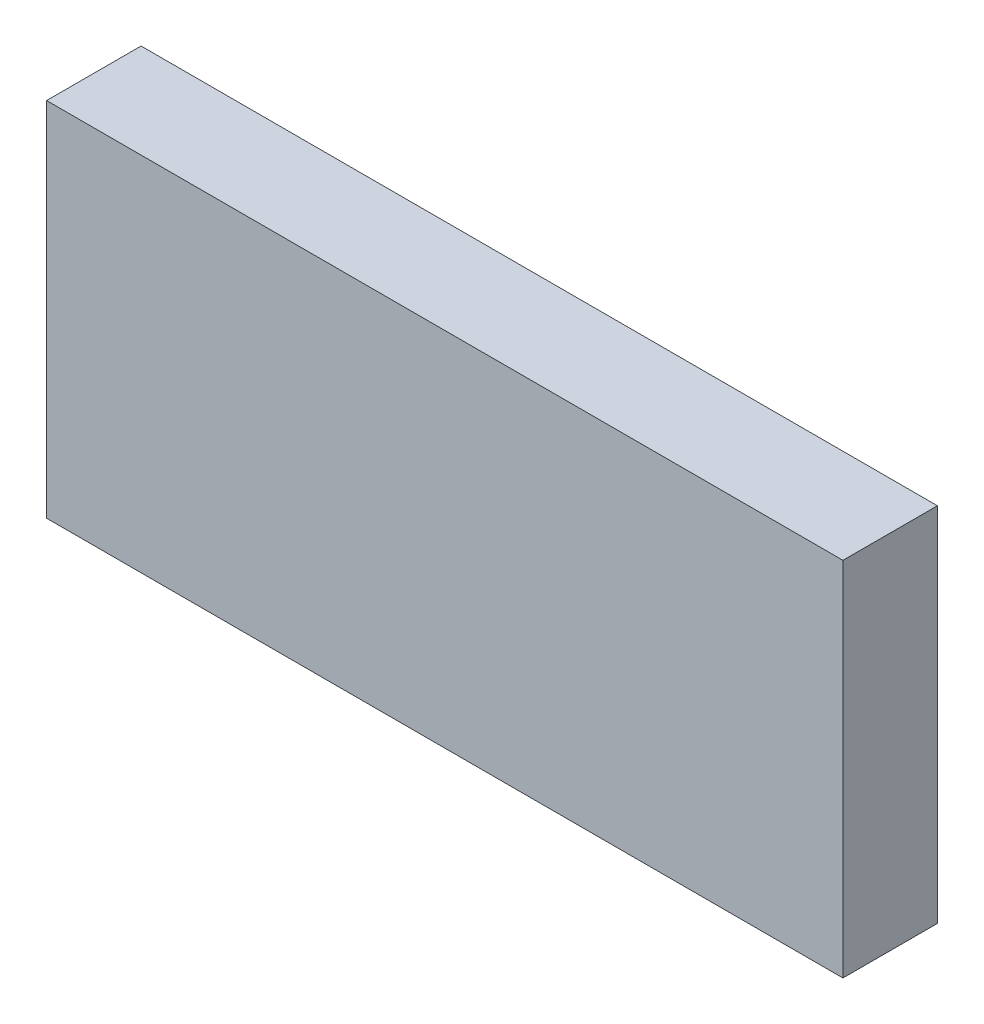
SolidWorks part; units mm, degrees
ref_plane "Front Plane" through (0, 0, 0) normal (0, 0, 1) x (1, 0, 0)
ref_plane "Top Plane" through (0, 0, 0) normal (0, 1, 0) x (1, 0, 0)
ref_plane "Right Plane" through (0, 0, 0) normal (1, 0, 0) x (0, 0, -1)
sketch "Sketch1" plane through (0, 0, 0) normal (0, 0, 1) x (1, 0, 0)
  line L0 (0, 0) -> (84.2977, 0)
  line L1 (84.2977, 0) -> (84.2977, 38.2926)
  line L2 (84.2977, 38.2926) -> (0, 38.2926)
  line L3 (0, 38.2926) -> (0, 0)
extrude "Boss-Extrude1" add sketch "Sketch1" along normal blind 10
